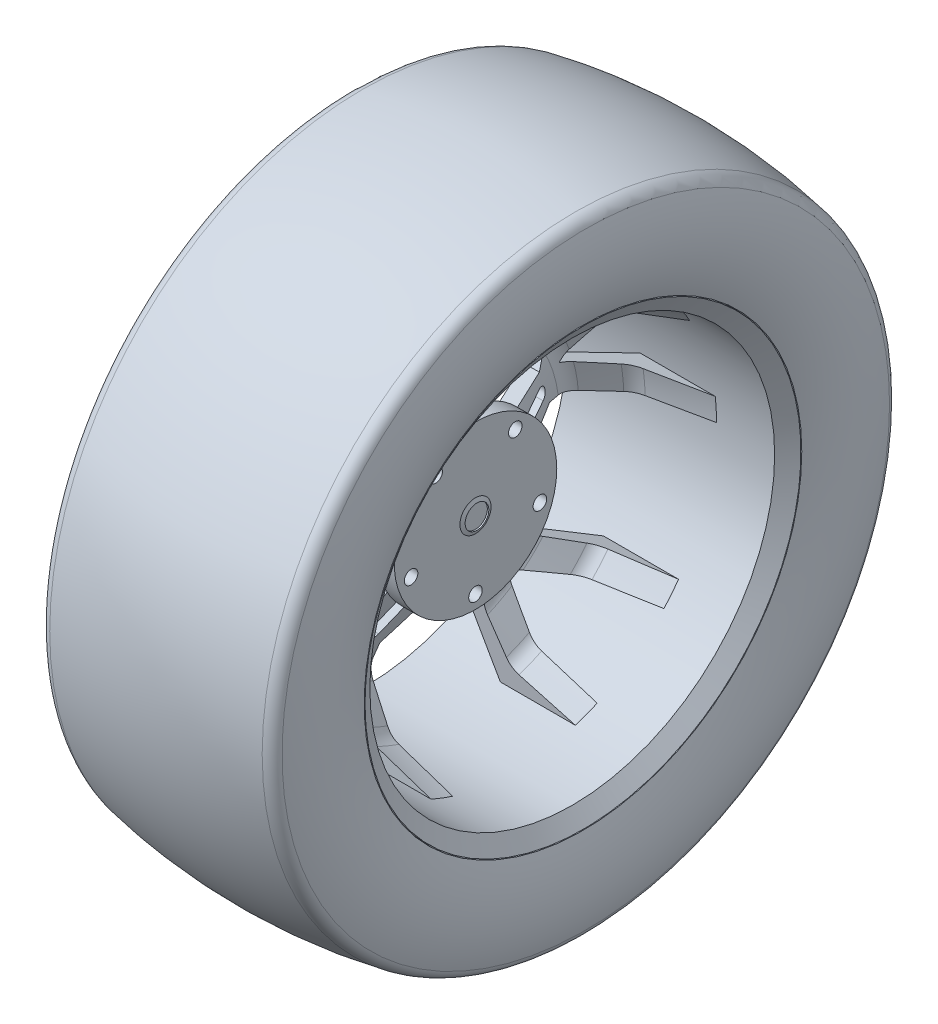
SolidWorks part; units mm, degrees
ref_plane "Front Plane" through (0, 0, 0) normal (0, 0, 1) x (1, 0, 0)
ref_plane "Top Plane" through (0, 0, 0) normal (0, 1, 0) x (1, 0, 0)
ref_plane "Right Plane" through (0, 0, 0) normal (1, 0, 0) x (0, 0, -1)
sketch "Sketch1" plane through (0, 0, 0) normal (0, 1, 0) x (1, 0, 0)
  line L0 (-50.3915, 0) -> (84.6916, 0) construction
  line L1 (0, 0) -> (0, 152.4) construction
  line L2 (0, 152.4) -> (-76.2, 152.4) construction
  line L3 (-84.1223, 160.8839) -> (-76.2, 149.4007)
  line L4 (-76.2, 149.4007) -> (-22.1546, 149.4007)
  line L5 (-84.1223, 160.8839) -> (-76.2, 160.8839)
  line L6 (-76.2, 160.8839) -> (-72.0646, 154.8898)
  line L7 (-72.0646, 154.8898) -> (72.0646, 154.8898)
  line L8 (84.1223, 160.8839) -> (76.2, 149.4007)
  line L9 (84.1223, 160.8839) -> (76.2, 160.8839)
  line L10 (76.2, 160.8839) -> (72.0646, 154.8898)
  line L11 (-22.1546, 149.4007) -> (-41.066, 109.0826)
  line L12 (-41.3929, 96.8875) -> (-5.6758, 8.7417)
  line L13 (-5.6758, 8.7417) -> (5.8944, 8.7417)
  line L14 (5.8944, 8.7417) -> (-29.5043, 96.1019)
  line L15 (-28.5284, 109.5305) -> (-16.2613, 130.4634)
  line L16 (-7.4342, 137.3725) -> (33.2422, 149.4007)
  line L17 (33.2422, 149.4007) -> (76.2, 149.4007)
  arc A0 (-16.2613, 130.4634) -> (-7.4342, 137.3725) centre (-3.1127, 122.7581) cw
  arc A1 (-29.5043, 96.1019) -> (-28.5284, 109.5305) centre (-15.3798, 101.8252) cw
  arc A2 (-41.066, 109.0826) -> (-41.3929, 96.8875) centre (-27.2684, 102.6108) ccw
  point P13 (0, 149.4007)
  point P16 (0, 154.8898)
  dimension "D1" = 15.24
revolve "Revolve2" add sketch "Sketch1" angle 360 about L0
ref_plane "Plane2" through (-84.1223, 0, 0) normal (1, 0, 0) x (0, 0, -1)
sketch "Sketch2" plane through (-84.1223, 0, 0) normal (1, 0, 0) x (0, 0, -1)
  line L0 (0, 0) -> (0, 149.4007) construction
  line L1 (30.4483, 146.2651) -> (0, 102.1805)
  line L2 (47.0317, 141.8048) -> (12.1455, 85.3463)
  line L3 (12.1455, 85.3463) -> (19.2781, 39.4819)
  line L4 (24.4631, 36.4969) -> (47.0317, 141.8048)
  line L5 (-30.4483, 146.2651) -> (0, 102.1805)
  line L6 (-24.4631, 36.4969) -> (-47.0317, 141.8048)
  line L7 (-12.1455, 85.3463) -> (-19.2781, 39.4819)
  line L8 (-47.0317, 141.8048) -> (-12.1455, 85.3463)
  line L9 (0, 29.3967) -> (0, 80.4389) construction
  line L10 (-4.5937, 29.3967) -> (-4.5937, 80.4389)
  line L11 (4.5937, 29.3967) -> (4.5937, 80.4389)
  arc A0 (-4.5937, 29.3967) -> (4.5937, 29.3967) centre (0, 29.3967) ccw
  arc A1 (30.4483, 146.2651) -> (-30.4483, 146.2651) centre (0, 0) ccw
  arc A2 (4.5937, 80.4389) -> (-4.5937, 80.4389) centre (0, 80.4389) ccw
  arc A3 (24.4631, 36.4969) -> (19.2781, 39.4819) centre (0, 0) ccw
  arc A4 (-19.2781, 39.4819) -> (-24.4631, 36.4969) centre (0, 0) ccw
  point P5 (30.4483, 146.2651)
  point P8 (47.0317, 141.8048)
  point P16 (0, 54.9178)
extrude "Cut-Extrude1" cut sketch "Sketch2" along normal blind 360.68
ref_axis "Axis1" through (72.0646, 0, 0) along (-1, 0, 0)
pattern_circular "CirPattern1" count 5 over 360 about axis through (0, 0, 0) along (1, 0, 0) of "Cut-Extrude1"
sketch "Sketch3" plane through (-84.1223, 0, 0) normal (1, 0, 0) x (0, 0, -1)
  line L0 (47.0317, 141.8048) -> (24.4631, 36.4969)
  line L1 (120.3308, 88.5498) -> (27.1511, 34.544)
  arc A0 (120.3308, 88.5498) -> (47.0317, 141.8048) centre (0, 0) ccw
  arc A1 (27.1511, 34.544) -> (24.4631, 36.4969) centre (0, 0) ccw
extrude "Cut-Extrude2" cut sketch "Sketch3" along normal blind 158.75
pattern_circular "CirPattern2" count 5 over 360 about axis through (72.0646, 0, 0) along (-1, 0, 0) of "Cut-Extrude2"
sketch "Sketch4" plane through (-84.1223, 0, 0) normal (1, 0, 0) x (0, 0, -1)
  line L0 (0, 0) -> (-29.3746, -9.6627) construction
  circle A0 centre (0, 0) radius 60
extrude "Boss-Extrude1" add sketch "Sketch4" along normal blind 12.7 from offset 76.2
sketch "Sketch5" plane through (4.7777, 0, 0) normal (1, 0, 0) x (0, 0, -1)
  line L0 (0, 0) -> (0, -50) construction
  circle A0 centre (0, -50) radius 5
extrude "Cut-Extrude3" cut sketch "Sketch5" against normal blind 66.802
pattern_circular "CirPattern3" count 5 over 360 about axis through (0, 0, 0) along (1, 0, 0) of "Cut-Extrude3"
sketch "Sketch6" plane through (0, 0, 0) normal (0, 1, 0) x (1, 0, 0)
  line L0 (-84.1223, 161.4925) -> (-84.1223, 229.9309) construction
  line L1 (-84.1223, -176.9723) -> (-84.1223, 176.9723) construction
  line L2 (-84.1223, 161.4925) -> (84.1223, 160.8839) construction
  line L3 (0, 161.1882) -> (0, 229.9309) construction
  line L4 (-84.1223, 161.4925) -> (-76.5259, 161.465)
  line L5 (-76.5259, 161.465) -> (-72.0646, 154.8898)
  line L6 (84.1223, 161.4925) -> (75.8579, 161.4925)
  line L7 (75.8579, 161.4925) -> (71.189, 155.2266)
  line L8 (-71.1284, 171.6056) -> (-63.6572, 160.5942)
  line L9 (-76.9227, 171.6265) -> (-71.1284, 171.6056)
  line L10 (76.9307, 171.6525) -> (70.758, 171.6525)
  line L11 (70.758, 171.6525) -> (63.042, 161.2971)
  line L12 (-72.0646, 154.8898) -> (-63.6572, 160.5942)
  line L13 (63.042, 161.2971) -> (71.189, 155.2266)
  arc A0 (-86.1928, 224.1849) -> (-84.1223, 161.4925) centre (1.8346, 195.7117) ccw
  arc A1 (86.1928, 224.1849) -> (84.1223, 161.4925) centre (-1.8346, 195.7117) cw
  arc A2 (-78.3971, 231.0443) -> (78.3971, 231.0443) centre (0, -187.3507) cw
  arc A3 (86.1928, 224.1849) -> (78.3971, 231.0443) centre (76.5259, 221.0581) ccw
  arc A4 (-86.1928, 224.1849) -> (-78.3971, 231.0443) centre (-76.5259, 221.0581) cw
  arc A5 (-76.5259, 221.0581) -> (-76.9227, 171.6265) centre (1.8346, 195.7117) ccw
  arc A6 (-76.5259, 221.0581) -> (-76.5259, 221.0581) centre (-76.5259, 221.0581) cw
  arc A7 (-76.5259, 221.0581) -> (76.5259, 221.0581) centre (0, -187.3507) cw
  arc A8 (76.5259, 221.0581) -> (76.5259, 221.0581) centre (76.5259, 221.0581) ccw
  arc A9 (76.5259, 221.0581) -> (76.9307, 171.6525) centre (-1.8346, 195.7117) cw
  point P16 (84.1223, 229.9309)
  dimension "D1" = 10.16
  dimension "D2" = 10.16
revolve "Revolve3" add sketch "Sketch6" angle 360 about axis through (72.0646, 0, 0) along (-1, 0, 0)
